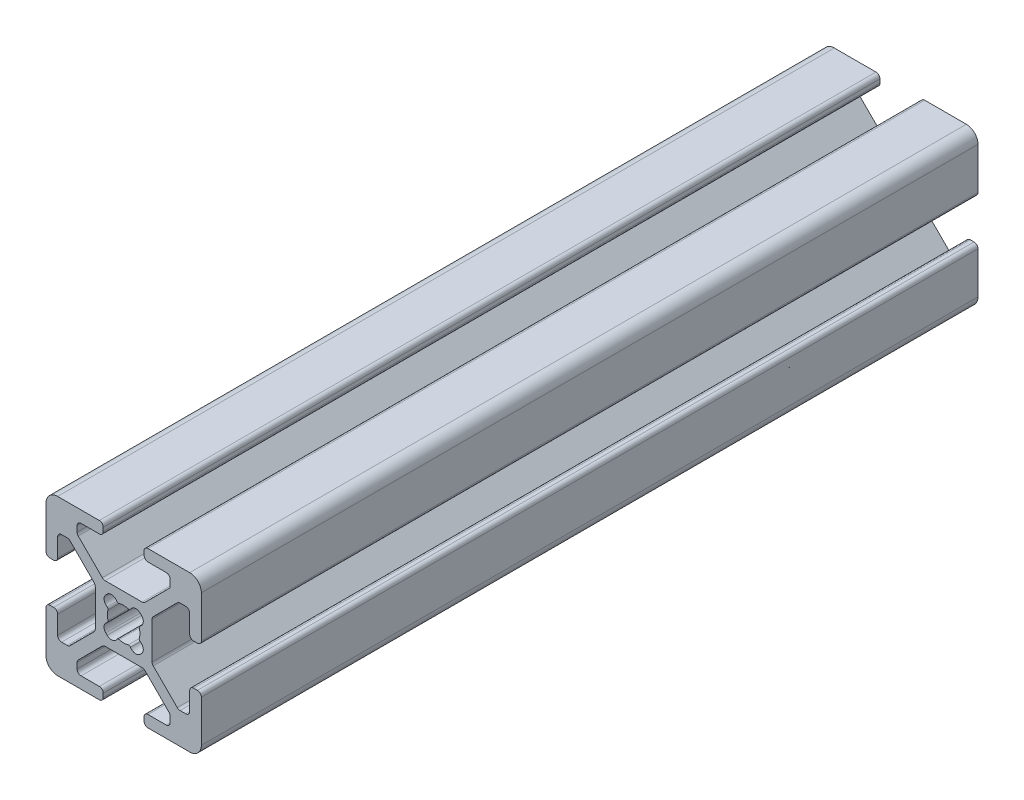
SolidWorks part; units mm, degrees
material "6105-T5 Aluminum"
ref_plane "Front Plane" through (0, 0, 0) normal (0, 0, 1) x (1, 0, 0)
ref_plane "Top Plane" through (0, 0, 0) normal (0, 1, 0) x (1, 0, 0)
ref_plane "Right Plane" through (0, 0, 0) normal (1, 0, 0) x (0, 0, -1)
sketch "Sketch1" plane through (0, 0, 0) normal (0, 0, 1) x (1, 0, 0)
  line L0 (9.0094, 2.6289) -> (9.492, 2.6289)
  line L1 (8.5014, 5.4864) -> (8.5014, 3.1369)
  line L2 (10, 8.5014) -> (10, 3.1369)
  line L3 (7.2645, 5.9944) -> (7.9934, 5.9944)
  line L4 (3.1369, 10) -> (8.5014, 10)
  line L5 (3.8074, 2.7477) -> (6.9053, 5.8456)
  line L6 (2.6289, 9.0094) -> (2.6289, 9.492)
  line L7 (3.6586, -2.3885) -> (3.6586, 2.3885)
  line L8 (3.1369, 8.5014) -> (5.4864, 8.5014)
  line L9 (6.9053, -5.8456) -> (3.8074, -2.7477)
  line L10 (5.9944, 7.9934) -> (5.9944, 7.2645)
  line L11 (7.9934, -5.9944) -> (7.2645, -5.9944)
  line L12 (5.8456, 6.9053) -> (2.7477, 3.8074)
  line L13 (8.5014, -3.1369) -> (8.5014, -5.4864)
  line L14 (2.3885, 3.6586) -> (-2.3885, 3.6586)
  line L15 (9.0094, -2.6289) -> (9.492, -2.6289)
  line L16 (-2.7477, 3.8074) -> (-5.8456, 6.9053)
  line L17 (10, -3.1369) -> (10, -8.5014)
  line L18 (-5.9944, 7.2645) -> (-5.9944, 7.9934)
  line L19 (8.5014, -10) -> (3.1369, -10)
  line L20 (-5.4864, 8.5014) -> (-3.1369, 8.5014)
  line L21 (2.6289, -9.0094) -> (2.6289, -9.492)
  line L22 (-2.6289, 9.0094) -> (-2.6289, 9.492)
  line L23 (5.4864, -8.5014) -> (3.1369, -8.5014)
  line L24 (-8.5014, 10) -> (-3.1369, 10)
  line L25 (5.9944, -7.2645) -> (5.9944, -7.9934)
  line L26 (-10, 3.1369) -> (-10, 8.5014)
  line L27 (2.7477, -3.8074) -> (5.8456, -6.9053)
  line L28 (-9.0094, 2.6289) -> (-9.492, 2.6289)
  line L29 (-2.3885, -3.6586) -> (2.3885, -3.6586)
  line L30 (-8.5014, 3.1369) -> (-8.5014, 5.4864)
  line L31 (-5.8456, -6.9053) -> (-2.7477, -3.8074)
  line L32 (-7.9934, 5.9944) -> (-7.2645, 5.9944)
  line L33 (-5.9944, -7.9934) -> (-5.9944, -7.2645)
  line L34 (-6.9053, 5.8456) -> (-3.8074, 2.7477)
  line L35 (-3.1369, -8.5014) -> (-5.4864, -8.5014)
  line L36 (-3.6586, 2.3885) -> (-3.6586, -2.3885)
  line L37 (-2.6289, -9.0094) -> (-2.6289, -9.492)
  line L38 (-3.8074, -2.7477) -> (-6.9053, -5.8456)
  line L39 (-3.1369, -10) -> (-8.5014, -10)
  line L40 (-7.2645, -5.9944) -> (-7.9934, -5.9944)
  line L41 (-10, -8.5014) -> (-10, -3.1369)
  line L42 (-8.5014, -5.4864) -> (-8.5014, -3.1369)
  line L43 (-9.0094, -2.6289) -> (-9.492, -2.6289)
  line L44 (-2.2966, 2.1217) -> (-2.1217, 2.2966)
  line L45 (2.1217, 2.2966) -> (2.2966, 2.1217)
  line L46 (-2.1217, -2.2966) -> (-2.2966, -2.1217)
  line L47 (2.2966, -2.1217) -> (2.1217, -2.2966)
  arc A0 (8.5014, 3.1369) -> (9.0094, 2.6289) centre (9.0094, 3.1369) ccw
  arc A1 (9.492, 2.6289) -> (10, 3.1369) centre (9.492, 3.1369) ccw
  arc A2 (8.5014, 5.4864) -> (7.9934, 5.9944) centre (7.9934, 5.4864) ccw
  arc A3 (10, 8.5014) -> (8.5014, 10) centre (8.5014, 8.5014) ccw
  arc A4 (7.2645, 5.9944) -> (6.9053, 5.8456) centre (7.2645, 5.4864) ccw
  arc A5 (3.1369, 10) -> (2.6289, 9.492) centre (3.1369, 9.492) ccw
  arc A6 (3.8074, 2.7477) -> (3.6586, 2.3885) centre (4.1666, 2.3885) ccw
  arc A7 (2.6289, 9.0094) -> (3.1369, 8.5014) centre (3.1369, 9.0094) ccw
  arc A8 (3.6586, -2.3885) -> (3.8074, -2.7477) centre (4.1666, -2.3885) ccw
  arc A9 (5.9944, 7.9934) -> (5.4864, 8.5014) centre (5.4864, 7.9934) ccw
  arc A10 (6.9053, -5.8456) -> (7.2645, -5.9944) centre (7.2645, -5.4864) ccw
  arc A11 (5.8456, 6.9053) -> (5.9944, 7.2645) centre (5.4864, 7.2645) ccw
  arc A12 (7.9934, -5.9944) -> (8.5014, -5.4864) centre (7.9934, -5.4864) ccw
  arc A13 (2.3885, 3.6586) -> (2.7477, 3.8074) centre (2.3885, 4.1666) ccw
  arc A14 (9.0094, -2.6289) -> (8.5014, -3.1369) centre (9.0094, -3.1369) ccw
  arc A15 (-2.7477, 3.8074) -> (-2.3885, 3.6586) centre (-2.3885, 4.1666) ccw
  arc A16 (10, -3.1369) -> (9.492, -2.6289) centre (9.492, -3.1369) ccw
  arc A17 (-5.9944, 7.2645) -> (-5.8456, 6.9053) centre (-5.4864, 7.2645) ccw
  arc A18 (8.5014, -10) -> (10, -8.5014) centre (8.5014, -8.5014) ccw
  arc A19 (-5.4864, 8.5014) -> (-5.9944, 7.9934) centre (-5.4864, 7.9934) ccw
  arc A20 (2.6289, -9.492) -> (3.1369, -10) centre (3.1369, -9.492) ccw
  arc A21 (-3.1369, 8.5014) -> (-2.6289, 9.0094) centre (-3.1369, 9.0094) ccw
  arc A22 (3.1369, -8.5014) -> (2.6289, -9.0094) centre (3.1369, -9.0094) ccw
  arc A23 (-2.6289, 9.492) -> (-3.1369, 10) centre (-3.1369, 9.492) ccw
  arc A24 (5.4864, -8.5014) -> (5.9944, -7.9934) centre (5.4864, -7.9934) ccw
  arc A25 (-8.5014, 10) -> (-10, 8.5014) centre (-8.5014, 8.5014) ccw
  arc A26 (5.9944, -7.2645) -> (5.8456, -6.9053) centre (5.4864, -7.2645) ccw
  arc A27 (-10, 3.1369) -> (-9.492, 2.6289) centre (-9.492, 3.1369) ccw
  arc A28 (2.7477, -3.8074) -> (2.3885, -3.6586) centre (2.3885, -4.1666) ccw
  arc A29 (-9.0094, 2.6289) -> (-8.5014, 3.1369) centre (-9.0094, 3.1369) ccw
  arc A30 (-2.3885, -3.6586) -> (-2.7477, -3.8074) centre (-2.3885, -4.1666) ccw
  arc A31 (-7.9934, 5.9944) -> (-8.5014, 5.4864) centre (-7.9934, 5.4864) ccw
  arc A32 (-5.8456, -6.9053) -> (-5.9944, -7.2645) centre (-5.4864, -7.2645) ccw
  arc A33 (-6.9053, 5.8456) -> (-7.2645, 5.9944) centre (-7.2645, 5.4864) ccw
  arc A34 (-5.9944, -7.9934) -> (-5.4864, -8.5014) centre (-5.4864, -7.9934) ccw
  arc A35 (-3.6586, 2.3885) -> (-3.8074, 2.7477) centre (-4.1666, 2.3885) ccw
  arc A36 (-2.6289, -9.0094) -> (-3.1369, -8.5014) centre (-3.1369, -9.0094) ccw
  arc A37 (-3.8074, -2.7477) -> (-3.6586, -2.3885) centre (-4.1666, -2.3885) ccw
  arc A38 (-3.1369, -10) -> (-2.6289, -9.492) centre (-3.1369, -9.492) ccw
  arc A39 (-7.2645, -5.9944) -> (-6.9053, -5.8456) centre (-7.2645, -5.4864) ccw
  arc A40 (-10, -8.5014) -> (-8.5014, -10) centre (-8.5014, -8.5014) ccw
  arc A41 (-8.5014, -5.4864) -> (-7.9934, -5.9944) centre (-7.9934, -5.4864) ccw
  arc A42 (-9.492, -2.6289) -> (-10, -3.1369) centre (-9.492, -3.1369) ccw
  arc A43 (-8.5014, -3.1369) -> (-9.0094, -2.6289) centre (-9.0094, -3.1369) ccw
  arc A44 (-0.8806, 2.1293) -> (-0.5885, 2.0112) centre (-0.6599, 2.2549) ccw
  arc A45 (0.5885, 2.0112) -> (-0.5885, 2.0112) centre (0, 0) ccw
  arc A46 (-0.8806, 2.1293) -> (-2.1217, 2.2966) centre (-1.565, 1.7398) ccw
  arc A47 (0.5885, 2.0112) -> (0.8806, 2.1293) centre (0.6599, 2.2549) ccw
  arc A48 (2.1217, 2.2966) -> (0.8806, 2.1293) centre (1.565, 1.7398) ccw
  arc A49 (-2.2966, 2.1217) -> (-2.1293, 0.8806) centre (-1.7398, 1.565) ccw
  arc A50 (-2.0112, 0.5885) -> (-2.1293, 0.8806) centre (-2.2549, 0.6599) ccw
  arc A51 (2.1293, 0.8806) -> (2.2966, 2.1217) centre (1.7398, 1.565) ccw
  arc A52 (-2.0112, 0.5885) -> (-2.0112, -0.5885) centre (0, 0) ccw
  arc A53 (2.1293, 0.8806) -> (2.0112, 0.5885) centre (2.2549, 0.6599) ccw
  arc A54 (-2.1293, -0.8806) -> (-2.0112, -0.5885) centre (-2.2549, -0.6599) ccw
  arc A55 (2.0112, -0.5885) -> (2.0112, 0.5885) centre (0, 0) ccw
  arc A56 (-2.1293, -0.8806) -> (-2.2966, -2.1217) centre (-1.7398, -1.565) ccw
  arc A57 (2.0112, -0.5885) -> (2.1293, -0.8806) centre (2.2549, -0.6599) ccw
  arc A58 (2.2966, -2.1217) -> (2.1293, -0.8806) centre (1.7398, -1.565) ccw
  arc A59 (-2.1217, -2.2966) -> (-0.8806, -2.1293) centre (-1.565, -1.7398) ccw
  arc A60 (-0.5885, -2.0112) -> (-0.8806, -2.1293) centre (-0.6599, -2.2549) ccw
  arc A61 (0.8806, -2.1293) -> (2.1217, -2.2966) centre (1.565, -1.7398) ccw
  arc A62 (-0.5885, -2.0112) -> (0.5885, -2.0112) centre (0, 0) ccw
  arc A63 (0.8806, -2.1293) -> (0.5885, -2.0112) centre (0.6599, -2.2549) ccw
extrude "Boss-Extrude1" add sketch "Sketch1" along normal blind 100
